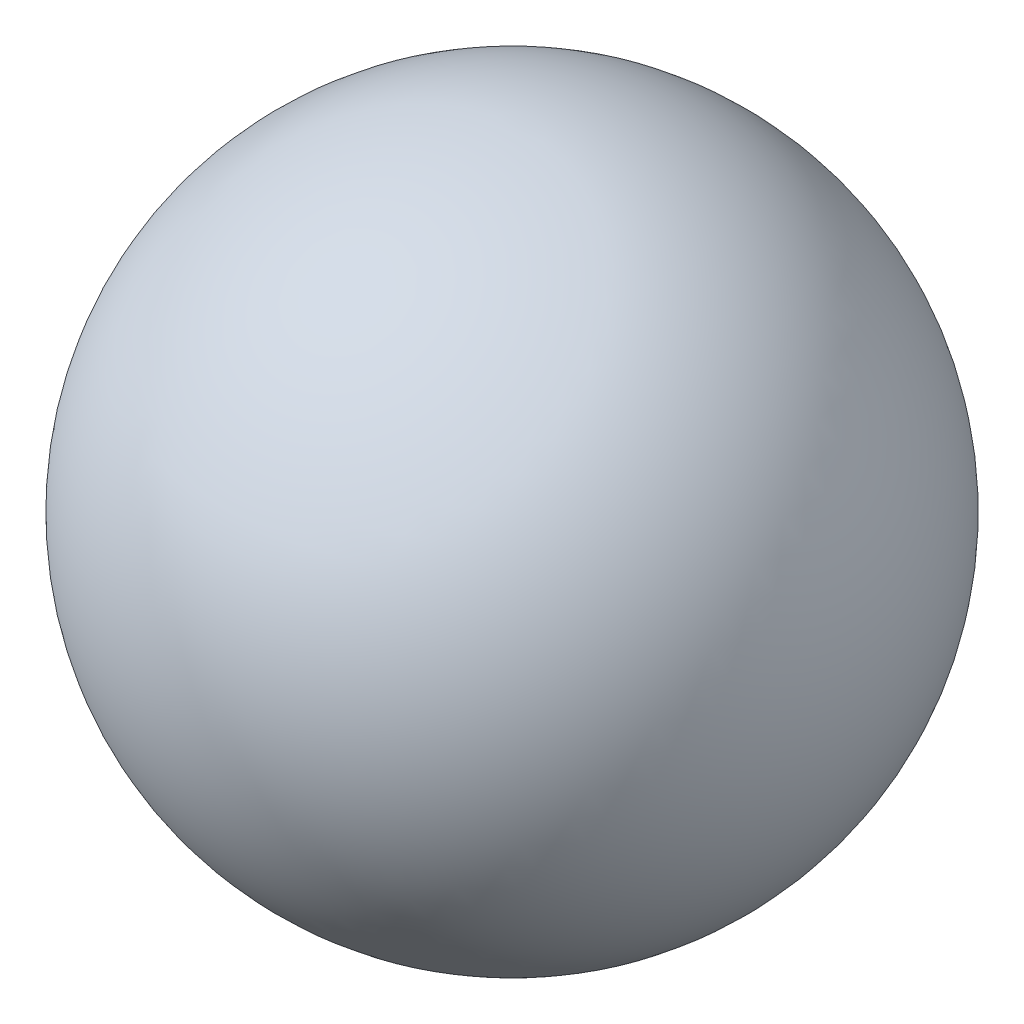
SolidWorks part; units mm, degrees
ref_plane "Front Plane" through (0, 0, 0) normal (0, 0, 1) x (1, 0, 0)
ref_plane "Top Plane" through (0, 0, 0) normal (0, 1, 0) x (1, 0, 0)
ref_plane "Right Plane" through (0, 0, 0) normal (1, 0, 0) x (0, 0, -1)
sketch "Sketch1" plane through (0, 0, 0) normal (0, 0, 1) x (1, 0, 0)
  line L0 (0, 9.525) -> (0, -9.525) construction
  circle A0 centre (0, 0) radius 9.525
  dimension "D1" = 19.05
revolve "Revolve7" add sketch "Sketch1" angle 360 about L0
